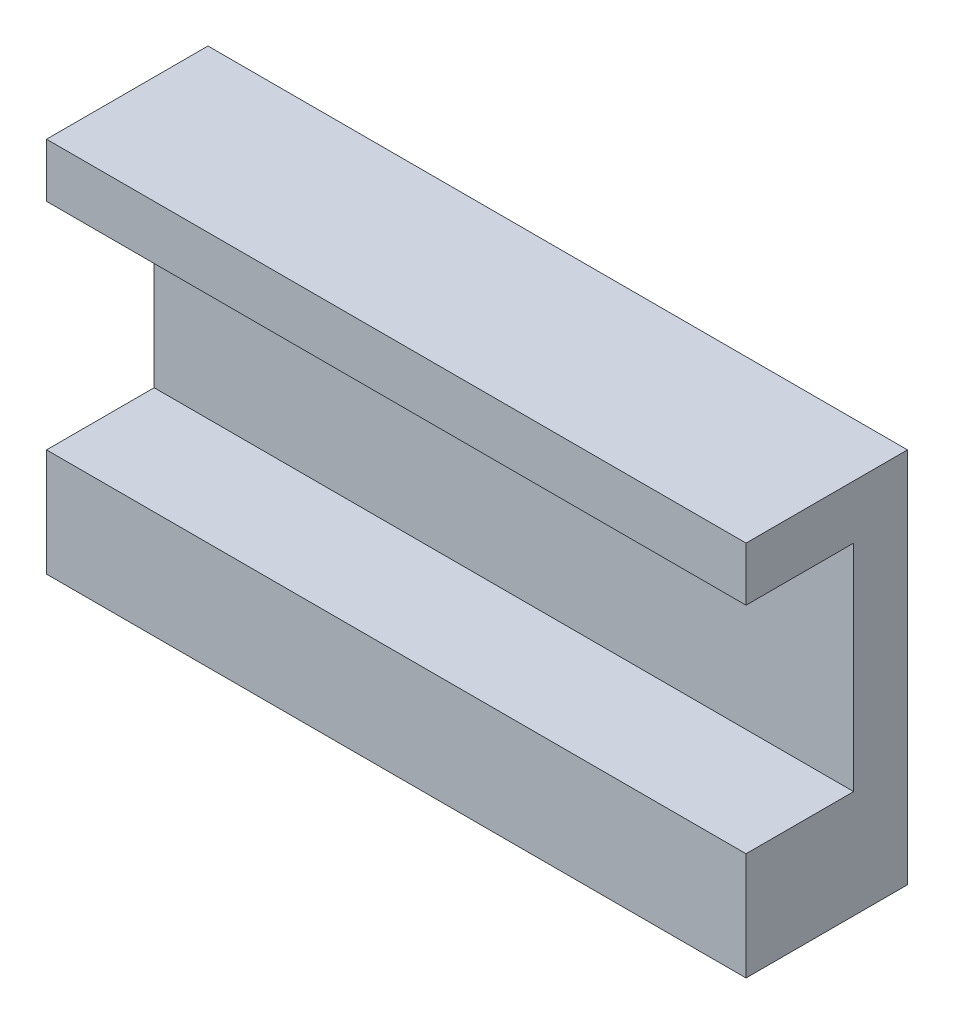
SolidWorks part; units mm, degrees
ref_plane "Front Plane" through (0, 0, 0) normal (0, 0, 1) x (1, 0, 0)
ref_plane "Top Plane" through (0, 0, 0) normal (0, 1, 0) x (1, 0, 0)
ref_plane "Right Plane" through (0, 0, 0) normal (1, 0, 0) x (0, 0, -1)
sketch "Sketch1" plane through (0, 0, 0) normal (0, 0, 1) x (1, 0, 0)
  line L1 (0, 0) -> (130, 0)
  line L2 (0, 0) -> (0, 70)
  line L3 (0, 70) -> (130, 70)
  line L4 (130, 0) -> (130, 70)
  dimension "D1" = 130
  dimension "D2" = 70
extrude "Boss-Extrude1" add sketch "Sketch1" along normal blind 10
sketch "Sketch2" plane through (0, 0, 10) normal (0, 0, 1) x (1, 0, 0)
  line L0 (0, 70) -> (0, 0) construction
  line L1 (130, 70) -> (0, 70)
  line L2 (130, 70) -> (130, 60)
  line L3 (130, 60) -> (0, 60)
  line L4 (0, 70) -> (0, 60)
  line L5 (130, 0) -> (130, 70) construction
  line L6 (0, 0) -> (130, 0)
  line L7 (0, 0) -> (0, 20)
  line L8 (0, 20) -> (130, 20)
  line L9 (130, 0) -> (130, 20)
  dimension "D1" = 10
  dimension "D2" = 20
extrude "Boss-Extrude2" add sketch "Sketch2" along normal blind 20
sketch "Sketch3" plane through (0, 0, 30) normal (0, 0, 1) x (1, 0, 0)
  line L0 (130, 20) -> (0, 20) construction
  line L1 (62.5, 20) -> (67.5, 20)
  line L2 (62.5, 20) -> (62.5, 0)
  line L3 (62.5, 0) -> (67.5, 0)
  line L4 (67.5, 20) -> (67.5, 0)
  line L5 (0, 0) -> (130, 0) construction
  line L6 (130, 70) -> (0, 70) construction
  point P8 (65, 20)
  point P11 (65, 70)
  dimension "D1" = 5
extrude "Boss-Extrude3" [suppressed] add sketch "Sketch3" along normal blind 10
ref_plane "Plane1" through (0, 0, 15) normal (0, 0, 1) x (1, 0, 0)
mirror "Mirror1" [suppressed] about plane through (0, 0, 15) normal (0, 0, 1)
